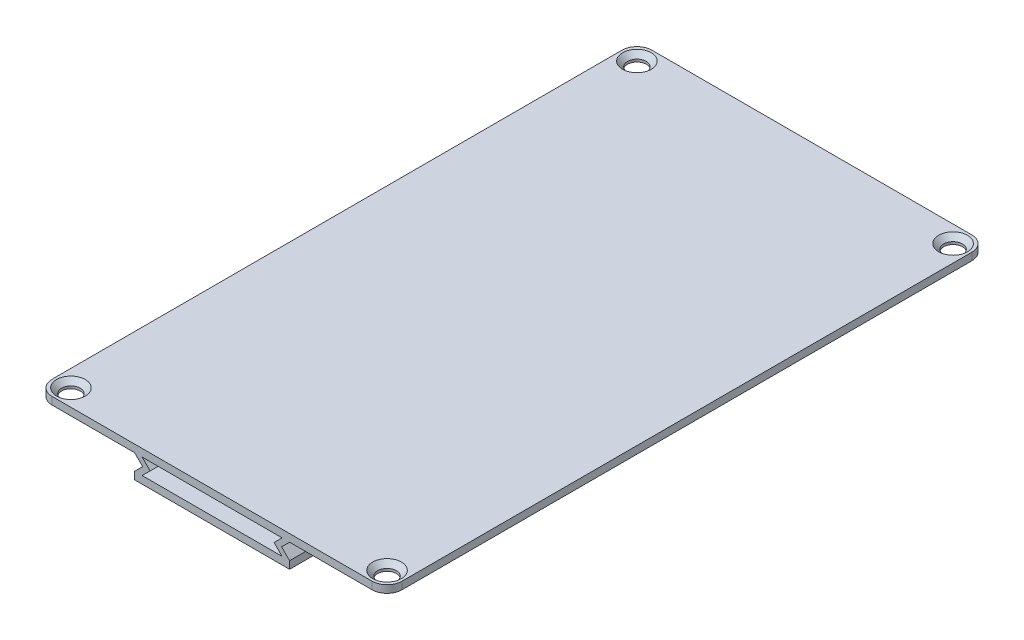
SolidWorks part; units mm, degrees
material "6061 Alloy"
ref_plane "Front Plane" through (0, 0, 0) normal (0, 0, 1) x (1, 0, 0)
ref_plane "Top Plane" through (0, 0, 0) normal (0, 1, 0) x (1, 0, 0)
ref_plane "Right Plane" through (0, 0, 0) normal (1, 0, 0) x (0, 0, -1)
sketch "Sketch2" plane through (0, 0, 0) normal (0, 0, 1) x (1, 0, 0)
  line L0 (0, 0) -> (-35, 0)
  line L1 (-35, 0) -> (-35, -1.5)
  line L2 (-35, -1.5) -> (-15.5, -1.5)
  line L3 (-15.5, -1.5) -> (-13.9, -3.1)
  line L4 (-13.9, -3.1) -> (-15.5, -4.7)
  line L5 (-15.5, -4.7) -> (-15.5, -6.2)
  line L6 (-15.5, -6.2) -> (0, -6.2)
  line L7 (0, 0) -> (0, -6.2) construction
  line L8 (0, -1.5) -> (-14, -1.5)
  line L9 (-14, -1.5) -> (-12.4, -3.1)
  line L10 (-12.4, -3.1) -> (-14, -4.7)
  line L11 (-14, -4.7) -> (0, -4.7)
  line L12 (-13.9, -3.1) -> (-12.4, -3.1) construction
  line L13 (0, 0) -> (0, -1.5)
  line L14 (0, -4.7) -> (0, -6.2)
  dimension "D1" = 35
  dimension "D2" = 1.5
  dimension "D3" = 6.2
  dimension "D4" = 31
extrude "Boss-Extrude1" add sketch "Sketch2" along normal mid plane 120
hole_wizard "M3 Clearance Hole1" positions "Sketch4" profile "Sketch6" hole size "M3" standard "ANSI Metric"
sketch "Sketch4" plane through (0, 0, 0) normal (0, 1, 0) x (1, 0, 0)
  line L0 (-31.4645, 56.4645) -> (-35, 60) construction
  line L2 (0, 0) -> (-35, 0) construction
  line L3 (0, -60) -> (0, 60) construction
  line L4 (-35, -60) -> (-35, 60) construction
  line L6 (0, 60) -> (-35, 60) construction
  point P0 (-31.4645, 56.4645)
  point P19 (-31.4645, -56.4645)
  dimension "D1" = 45
  dimension "D2" = 5
sketch "Sketch6" plane through (-31.4645, 0, -56.4645) normal (1, 0, 0) x (0, 0, 1)
  line L0 (0, 0) -> (0, 6.2)
  line L1 (0, 6.2) -> (1.8, 6.2)
  line L2 (1.8, 6.2) -> (1.8, 0)
  line L5 (1.8, 0) -> (0, 0)
  line L11 (0, -6.35) -> (0, 107.95) construction
  dimension "Thru Hole Dia." = 3.6
  dimension "Thru Hole Depth" = 6.2
sketch "Sketch7" plane through (0, 0, 0) normal (0, 1, 0) x (1, 0, 0)
  line L0 (0, 0) -> (-35, 0) construction
  line L1 (-35, -60) -> (-35, 60) construction
  line L2 (-35, 60) -> (-31.625, 56.625) construction
  line L3 (0, 60) -> (-35, 60) construction
  line L4 (0, -60) -> (0, 60) construction
  circle A0 centre (-31.625, 56.625) radius 1.875
  circle A1 centre (-31.625, -56.625) radius 1.875
  point P11 (-29.75, 56.625)
  point P12 (-33.5, 56.625)
  dimension "D1" = 45
  dimension "D2" = 29.75
  dimension "D3" = 33.5
extrude "Cut-Extrude1" cut sketch "Sketch7" against normal through all both and the other way through all
mirror "Mirror1" about plane through (0, -4.7, 60) normal (-1, 0, 0) of "Cut-Extrude1", "Boss-Extrude1"
chamfer "Chamfer1" distance 1 angle 45 4 edges at (-31.625, 0, 54.75) (31.625, 0, 54.75) (31.625, 0, -58.5) (-31.625, 0, -58.5)
fillet "Fillet1" radius 3 4 edges at (-35, -0.75, -60) (35, -0.75, -60) (35, -0.75, 60) (-35, -0.75, 60)
